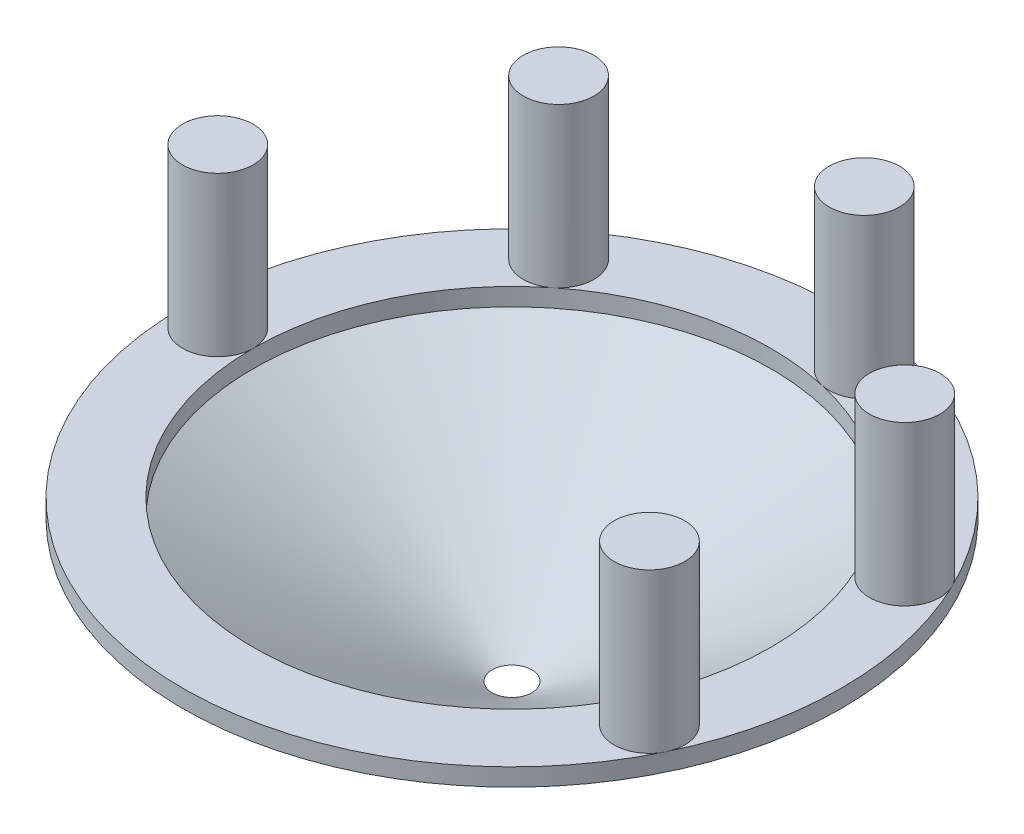
SolidWorks part; units mm, degrees
ref_plane "Front Plane" through (0, 0, 0) normal (0, 0, 1) x (1, 0, 0)
ref_plane "Top Plane" through (0, 0, 0) normal (0, 1, 0) x (1, 0, 0)
ref_plane "Right Plane" through (0, 0, 0) normal (1, 0, 0) x (0, 0, -1)
sketch "Sketch1" plane through (0, 0, 0) normal (0, 0, 1) x (1, 0, 0)
  line L0 (0, -582.4468) -> (0, 28539.8911) construction
  line L2 (28, 0) -> (3.175, -12)
  line L3 (3.175, -12) -> (1.686, -12)
  line L4 (1.686, -12) -> (22, 0)
  line L5 (1.686, -12) -> (0, -12) construction
  line L6 (22, 0) -> (0, 0) construction
  line L7 (22, 0) -> (22, 1.5)
  line L8 (22, 1.5) -> (28, 1.5)
  line L9 (28, 1.5) -> (28, 0)
  dimension "D1" = 1.489
  dimension "D2" = 1.686
  dimension "D3" = 22
  dimension "D4" = 6
  dimension "D5" = 12
  dimension "D6" = 1.5
revolve "Revolve1" add sketch "Sketch1" angle 360 about L0
sketch "Sketch3" plane through (0, 0, 0) normal (0, 1, 0) x (1, 0, 0)
  line L0 (-22, 0) -> (-28, 0) construction
  circle A1 centre (0, 0) radius 22 construction
  circle A2 centre (0, 0) radius 22 construction
  circle A3 centre (0, 0) radius 28 construction
  circle A4 centre (-25, 0) radius 3
extrude "Boss-Extrude1" add sketch "Sketch3" along normal blind 15
pattern_circular "CirPattern1" count 5 every 51.429 about axis through (0, 0, 0) along (0, 1, 0) of "Boss-Extrude1"
